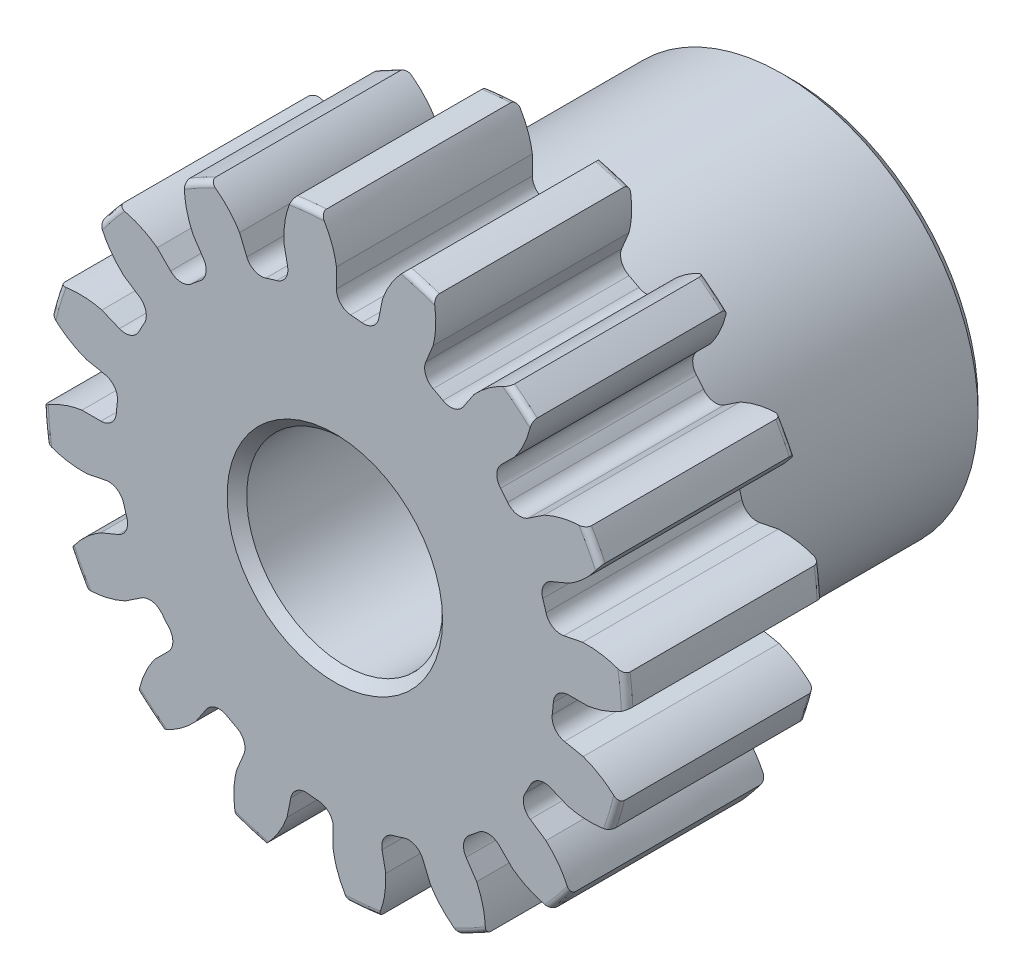
SolidWorks part; units mm, degrees
ref_plane "Front" through (0, 0, 0) normal (0, 0, 1) x (1, 0, 0)
ref_plane "Top" through (0, 0, 0) normal (0, 1, 0) x (1, 0, 0)
ref_plane "Right" through (0, 0, 0) normal (1, 0, 0) x (0, 0, -1)
sketch "Sketch1" plane through (0, 0, 0) normal (0, 0, 1) x (1, 0, 0)
  line L0 (-203.2, 0) -> (203.2, 0) construction
  circle A0 centre (0, 0) radius 7.112
  circle A1 centre (0, 0) radius 6.35 construction
  circle A3 centre (0, 0) radius 5.3261 construction
  dimension "D3" = 0.762
  dimension "D1" = 1.7859
extrude "Boss-Extrude1" add sketch "Sketch1" against normal blind 4.7625
sketch "Sketch2" plane through (0, 0, 0) normal (1, 0, 0) x (0, 0, -1)
  line L0 (4.7625, 0) -> (11.1125, 0)
  line L1 (4.7625, 0) -> (4.7625, 4.7625)
  line L2 (4.7625, 4.7625) -> (11.1125, 4.7625)
  line L3 (11.1125, 4.7625) -> (11.1125, 0)
  point P5 (11.1125, -4.7625)
  point P6 (0, -7.112)
  point P7 (4.7625, -7.112)
  point P9 (0, 7.112)
revolve "Revolve1" add sketch "Sketch2" angle 360 mid plane about L0
fillet "Fillet2" radius 0.1422 3 edges at (7.112, 0, -4.7625) (7.112, 0, 0) (4.7625, 0, -4.7625)
sketch "Sketch3" plane through (0, 0, 0) normal (0, 0, 1) x (1, 0, 0)
  line L0 (0, 0) -> (0, 7.112) construction
  line L1 (-1.5393, 5.9519) -> (0, 6.35)
  line L2 (-9.5921, 6.35) -> (9.5921, 6.35) construction
  line L3 (-9.2865, 3.9483) -> (9.2865, 8.7517) construction
  line L4 (-1.5393, 5.9519) -> (0, 0) construction
  line L5 (-3.9262, 4.7307) -> (0, 0) construction
  line L6 (-3.9262, 4.7307) -> (-0.6424, 7.456) construction
  line L7 (-1.0733, 6.0533) -> (0, 0) construction
  line L8 (-1.0733, 6.0533) -> (0.0225, 6.2476) construction
  arc A0 (-1.5393, 5.9519) -> (-3.9262, 4.7307) centre (0, 0) ccw
  circle A1 centre (0, 0) radius 6.35 construction
  circle A2 centre (0, 0) radius 6.1477 construction
  arc A3 (-1.5393, 5.9519) -> (-1.0733, 6.0533) centre (0, 0) cw
  circle A4 centre (0, 0) radius 7.112 construction
  point P6 (0, 6.35)
  dimension "D1" = 1.5899
  dimension "D3" = 4.2674
  dimension "D5" = 1.1129
  dimension "D2" = 2.7029
  dimension "D4" = 0.477
sketch "Sketch4" plane through (0, 0, 0) normal (0, 0, 1) x (1, 0, 0)
  line L0 (0, 0) -> (0.6194, 6.289) construction
  line L1 (0.0398, 6.1476) -> (0.0398, 5.3259)
  line L2 (0, 6.35) -> (1.2388, 6.228) construction
  line L3 (1.1603, 6.0372) -> (1, 5.2313)
  line L4 (0.0398, 5.3259) -> (0, 0) construction
  line L5 (0, 0) -> (0, 7.112) construction
  line L6 (-3.9262, 4.7307) -> (-0.6424, 7.456) construction
  line L7 (-3.9262, 4.7307) -> (-0.6424, 7.456) construction
  arc A0 (1, 5.2313) -> (0.0398, 5.3259) centre (0, 0) ccw
  arc A1 (0, 6.35) -> (1.2388, 6.228) centre (0, 0) cw construction
  circle A2 centre (0, 0) radius 6.35 construction
  circle A3 centre (0, 0) radius 6.1477 construction
  circle A4 centre (0, 0) radius 5.3261 construction
  arc A5 (2.0846, 7.1874) -> (-0.6424, 7.456) centre (0, 0) ccw
  spline S0 degree 2 poles (-0.6424, 7.456) (-0.0701, 6.8828) (0.0398, 6.1476) knots 0 0 0 1 1 1
  spline S1 degree 2 poles (2.0846, 7.1874) (1.4115, 6.7368) (1.1603, 6.0372) knots 0 0 0 1 1 1
  dimension "D1" = 1.2468
extrude "Cut-Extrude1" cut sketch "Sketch4" against normal through all
fillet "Fillet1" radius 0.374 2 edges at (1, 5.2313, -2.3813) (0.0398, 5.3259, -2.3813)
pattern_circular "CirPattern1" count 16 over 360 about axis through (0, 0, -4.7625) along (0, 0, 1) of "Cut-Extrude1", "Fillet1"
sketch "Sketch5" plane through (0, 0, 0) normal (0, 0, 1) x (1, 0, 0)
  circle A0 centre (0, 0) radius 2.3813
  circle A1 centre (0, 0) radius 1.5875 construction
  dimension "Bore Min" = 4.7625
  dimension "Bore Max" = 3.175
extrude "Cut-Extrude2" cut sketch "Sketch5" against normal through all
chamfer "Chamfer1" distance 0.2381 angle 45 3 edges at (4.7625, 0, -11.1125) (2.3813, 0, 0) (2.3813, 0, -11.1125)
sketch "Pitch Dia" plane through (0, 0, 0) normal (0, 0, 1) x (1, 0, 0)
  circle A0 centre (0, 0) radius 6.35 construction
  circle A1 centre (0, 0) radius 6.35 construction
equation "\"D1@Boss-Extrude1\" = \"Face Wd@Sketch2\""
equation "\"D2@Sketch3\" = \"D1@Sketch3\"*1.7"
equation "\"D3@Sketch3\" = \"D1@Sketch3\"+\"D2@Sketch3\"-.001"
equation "\"D4@Sketch3\" = \"D1@Sketch3\"*.3"
equation "\"D5@Sketch3\" = \"D1@Sketch3\"-\"D4@Sketch3\""
equation "\"D1@Sketch4\" = 1.5708/(\"Number of Teeth@Sketch1\"/\"Ptich Dia@Sketch1\")"
equation "\"D1@Chamfer1\" = \"B Hub Dia@Sketch2\"*.025"
equation "\"D1@CirPattern1\" = \"Number of Teeth@Sketch1\""
equation "\"D1@Fillet1\" = \"D1@Sketch4\"*.3"
equation "\"D1@Fillet2\" = \"OD@Sketch1\"*.01"
equation "\"D1@Sketch1\" = 2.250/(\"Number of Teeth@Sketch1\"/\"Ptich Dia@Sketch1\")"
